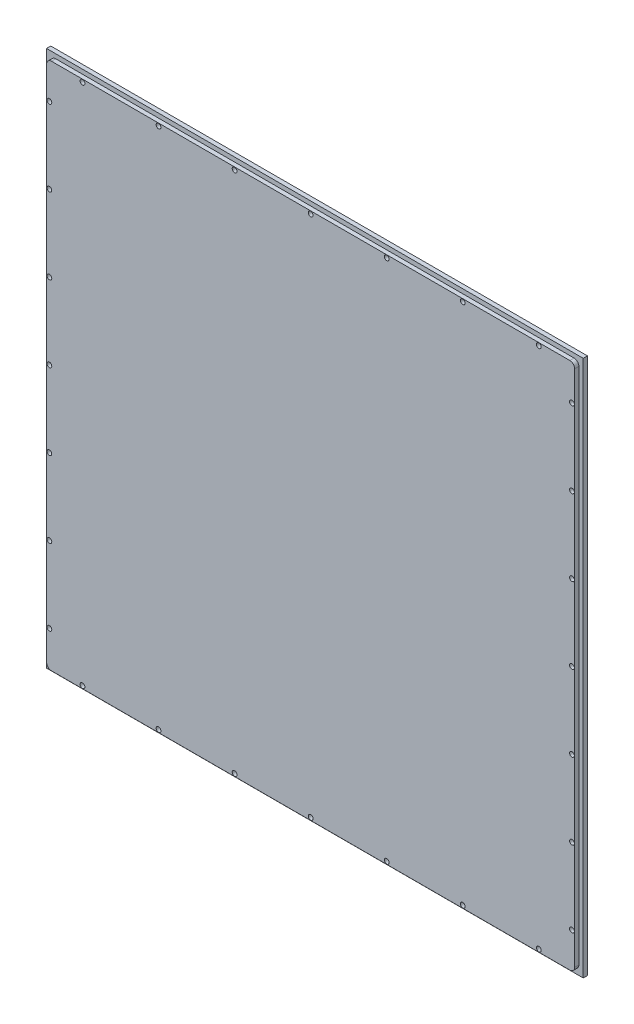
SolidWorks part; units mm, degrees
ref_plane "Plan de face" through (0, 0, 0) normal (0, 0, 1) x (1, 0, 0)
ref_plane "Plan de dessus" through (0, 0, 0) normal (0, 1, 0) x (1, 0, 0)
ref_plane "Plan de droite" through (0, 0, 0) normal (1, 0, 0) x (0, 0, -1)
sketch "Esquisse1" plane through (0, 0, 0) normal (0, 0, 1) x (1, 0, 0)
  line L1 (0, 381) -> (381, 381)
  line L2 (0, 381) -> (0, 0)
  line L3 (0, 0) -> (381, 0)
  line L4 (381, 381) -> (381, 0)
extrude "Boss.-Extru.1" add sketch "Esquisse1" along normal blind 3
sketch "Esquisse2" plane through (0, 0, 3) normal (0, 0, 1) x (1, 0, 0)
  line L0 (0, 0) -> (381, 0) construction
  line L7 (0, 3.1) -> (3.1, 3.1) construction
  line L8 (3.1, 0) -> (3.1, 3.1) construction
  line L13 (6.5, 3.1) -> (374.5, 3.1)
  line L14 (3.1, 6.5) -> (3.1, 374.5)
  line L15 (6.5, 377.9) -> (374.5, 377.9)
  line L16 (377.9, 6.5) -> (377.9, 374.5)
  line L17 (377.9, 381) -> (377.9, 377.9) construction
  line L18 (381, 381) -> (0, 381) construction
  line L19 (377.9, 377.9) -> (381, 377.9) construction
  line L20 (381, 0) -> (381, 381) construction
  arc A4 (374.5, 3.1) -> (377.9, 6.5) centre (374.5, 6.5) ccw
  arc A5 (6.5, 3.1) -> (3.1, 6.5) centre (6.5, 6.5) cw
  arc A6 (3.1, 374.5) -> (6.5, 377.9) centre (6.5, 374.5) cw
  arc A7 (374.5, 377.9) -> (377.9, 374.5) centre (374.5, 374.5) cw
  dimension "D1" = 3.4
extrude "Boss.-Extru.2" add sketch "Esquisse2" along normal blind 3
sketch "Esquisse8" plane through (0, 0, 0) normal (0, 0, 1) x (1, 0, 0)
  point P0 (5, 352.5)
  point P3 (28.5, 376)
  point P6 (82.5, 376)
  point P9 (136.5, 376)
  point P12 (190.5, 376)
  point P14 (244.5, 376)
  point P17 (298.5, 376)
  point P20 (352.5, 376)
  point P22 (376, 352.5)
  point P25 (376, 298.5)
  point P28 (376, 244.5)
  point P31 (376, 190.5)
  point P34 (376, 136.5)
  point P37 (376, 82.5)
  point P40 (376, 28.5)
  point P43 (352.5, 5)
  point P46 (298.5, 5)
  point P49 (244.5, 5)
  point P52 (190.5, 5)
  point P55 (136.5, 5)
  point P58 (82.5, 5)
  point P61 (28.5, 5)
  point P64 (5, 28.5)
  point P67 (5, 82.5)
  point P70 (5, 136.5)
  point P73 (5, 190.5)
  point P76 (5, 244.5)
  point P79 (5, 298.5)
hole_wizard "Fraisage pour vis à tête fraisée M31" positions "Esquisse9" profile "Esquisse10" countersink size "M3" standard "Ansi Metric" end condition through all
sketch "Esquisse9" plane through (0, 0, 0) normal (0, 0, -1) x (-1, 0, 0)
  point P0 (-28.5, 5)
  point P3 (-82.5, 5)
  point P6 (-136.5, 5)
  point P9 (-190.5, 5)
  point P12 (-244.5, 5)
  point P15 (-298.5, 5)
  point P18 (-352.5, 5)
  point P21 (-376, 28.5)
  point P24 (-376, 82.5)
  point P27 (-376, 136.5)
  point P30 (-376, 190.5)
  point P33 (-376, 244.5)
  point P36 (-376, 298.5)
  point P39 (-376, 352.5)
  point P42 (-352.5, 376)
  point P45 (-298.5, 376)
  point P48 (-244.5, 376)
  point P51 (-190.5, 376)
  point P54 (-136.5, 376)
  point P57 (-82.5, 376)
  point P60 (-28.5, 376)
  point P63 (-5, 352.5)
  point P66 (-5, 298.5)
  point P69 (-5, 244.5)
  point P72 (-5, 190.5)
  point P75 (-5, 136.5)
  point P78 (-5, 82.5)
  point P81 (-5, 28.5)
sketch "Esquisse10" plane through (28.5, 5, 0) normal (1, 0, 0) x (0, 1, 0)
  line L0 (0, 0) -> (0, 6)
  line L1 (0, 6) -> (1.7, 6)
  line L2 (1.7, 6) -> (1.7, 1.45)
  line L3 (1.7, 1.45) -> (3.15, 0)
  line L5 (3.15, 0) -> (0, 0)
  line L6 (-1.7, 1.45) -> (-3.15, 0) construction
  line L11 (0, -6.35) -> (0, 107.95) construction
  dimension "Diamètre du perçage jusqu'au prochain" = 3.4
  dimension "Profondeur du perçage jusqu'au prochain" = 6
  dimension "Diamètre du fraisage entrant" = 6.3
  dimension "Angle du fraisage entrant" = 90
